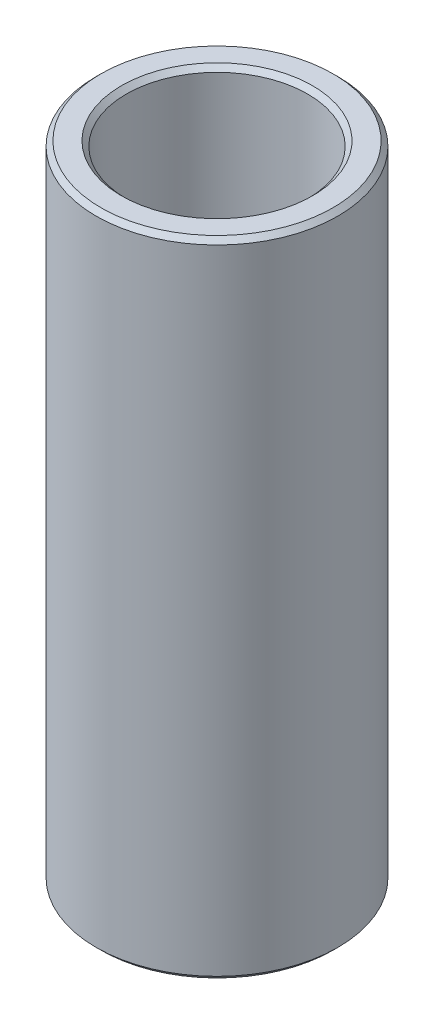
SolidWorks part; units mm, degrees
ref_plane "Front Plane" through (0, 0, 0) normal (0, 0, 1) x (1, 0, 0)
ref_plane "Top Plane" through (0, 0, 0) normal (0, 1, 0) x (1, 0, 0)
ref_plane "Right Plane" through (0, 0, 0) normal (1, 0, 0) x (0, 0, -1)
sketch "Sketch1" plane through (0, 0, 0) normal (0, 0, 1) x (1, 0, 0)
  line L0 (4.7625, 70.6437) -> (4.7625, 104.4199)
  line L1 (4.7625, 104.4199) -> (6.35, 104.4199)
  line L2 (6.35, 104.4199) -> (6.35, 70.6437)
  line L3 (6.35, 70.6437) -> (4.7625, 70.6437)
  line L4 (-10.0875, 79.3749) -> (-120.0875, 79.3749) construction
  line L6 (0, 61.1187) -> (0, 113.9449) construction
  dimension "D1" = 9.525
  dimension "D2" = 9.525
  dimension "D3" = 12.7
  dimension "D4" = 9.525
revolve "Revolve1" add sketch "Sketch1" angle 360 about L6
chamfer "Chamfer1" distance 0.254 angle 45 4 edges at (6.35, 104.4199, 0) (4.7625, 104.4199, 0) (4.7625, 70.6437, 0) (6.35, 70.6437, 0)
equation "\"D4@Sketch1\"=\"D1@Sketch1\""
